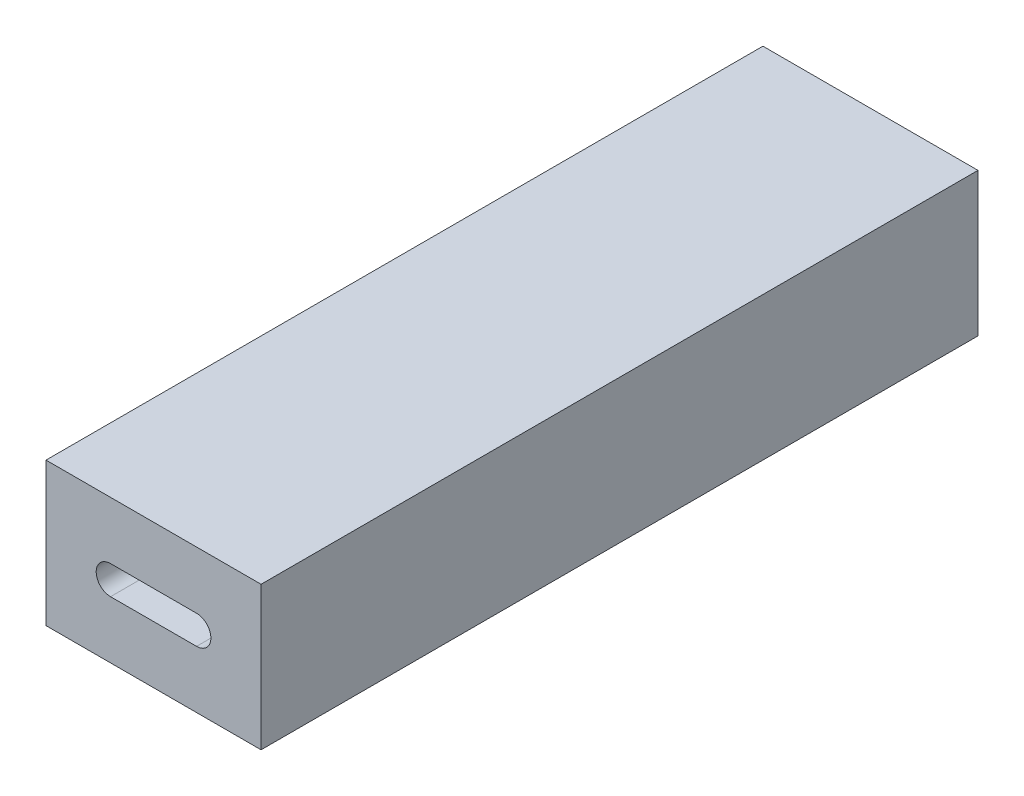
SolidWorks part; units mm, degrees
ref_plane "Alzado" through (0, 0, 0) normal (0, 0, 1) x (1, 0, 0)
ref_plane "Planta" through (0, 0, 0) normal (0, 1, 0) x (1, 0, 0)
ref_plane "Vista lateral" through (0, 0, 0) normal (1, 0, 0) x (0, 0, -1)
sketch "Sketch1" plane through (0, 0, 0) normal (0, 0, 1) x (1, 0, 0)
  line L1 (-7.5, 5) -> (7.5, 5)
  line L2 (-7.5, 5) -> (-7.5, -5)
  line L3 (-7.5, -5) -> (7.5, -5)
  line L4 (7.5, 5) -> (7.5, -5)
  dimension "D1" = 15
  dimension "D2" = 10
  dimension "D3" = 7.5
  dimension "D4" = 5
extrude "Boss-Extrude1" add sketch "Sketch1" along normal blind 50
sketch "Sketch2" plane through (0, 0, 50) normal (0, 0, 1) x (1, 0, 0)
  line L1 (-3, 1) -> (3, 1)
  line L6 (-3, -1) -> (3, -1)
  line L7 (-7.5, 5) -> (-7.5, -5) construction
  line L8 (-7.5, -5) -> (7.5, -5) construction
  arc A0 (-3, 1) -> (-3, -1) centre (-3, 0) ccw
  arc A1 (3, -1) -> (3, 1) centre (3, 0) ccw
  dimension "D2" = 1
  dimension "D3" = 1
  dimension "D1" = 6
  dimension "D4" = 4.5
  dimension "D5" = 4
extrude "Cut-Extrude1" cut sketch "Sketch2" against normal blind 25
sketch "Sketch3" plane through (0, 0, 0) normal (0, 0, -1) x (-1, 0, 0)
  circle A0 centre (0, 0) radius 2
  dimension "D1" = 4
extrude "Cut-Extrude2" cut sketch "Sketch3" against normal blind 25
